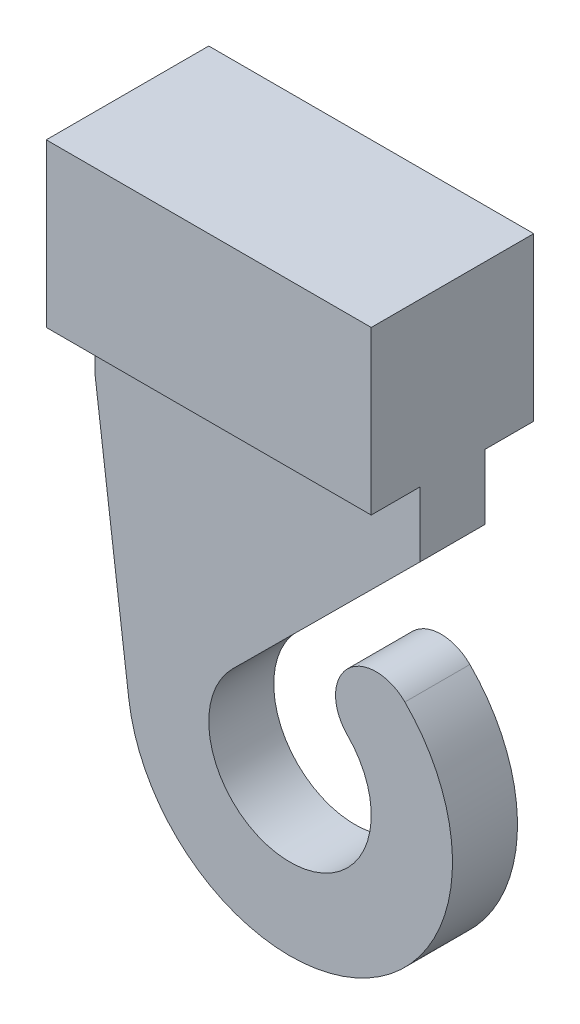
SolidWorks part; units mm, degrees
ref_plane "前视基准面" through (0, 0, 0) normal (0, 0, 1) x (1, 0, 0)
ref_plane "上视基准面" through (0, 0, 0) normal (0, 1, 0) x (1, 0, 0)
ref_plane "右视基准面" through (0, 0, 0) normal (1, 0, 0) x (0, 0, -1)
other "Configuration Table"
sketch "草图1" plane through (0, 0, 0) normal (1, 0, 0) x (0, 0, -1)
  line L1 (-1.5, 1.5) -> (1.5, 1.5)
  line L2 (-1.5, 1.5) -> (-1.5, -1.5)
  line L3 (-1.5, -1.5) -> (1.5, -1.5)
  line L4 (1.5, 1.5) -> (1.5, -1.5)
  line L5 (-1.5, 1.5) -> (1.5, -1.5) construction
  line L6 (-1.5, -1.5) -> (1.5, 1.5) construction
  line L7 (-2.5, 2.5) -> (2.5, 2.5)
  line L8 (-2.5, 2.5) -> (-2.5, -2.5)
  line L9 (-2.5, -2.5) -> (2.5, -2.5)
  line L10 (2.5, 2.5) -> (2.5, -2.5)
  line L11 (-2.5, 2.5) -> (2.5, -2.5) construction
  line L12 (-2.5, -2.5) -> (2.5, 2.5) construction
  point P0 (0, 0)
  point P6 (0, 0)
  dimension "D1" = 3
  dimension "D2" = 3
  dimension "D3" = 5
  dimension "D4" = 5
extrude "凸台-拉伸1" add sketch "草图1" along normal blind 8
sketch "草图2" plane through (8, 0, 0) normal (1, 0, 0) x (0, 0, -1)
  line L4 (2.5, -2.5) -> (2.5, 2.5)
  line L5 (2.5, 2.5) -> (-2.5, 2.5)
  line L6 (-2.5, 2.5) -> (-2.5, -2.5)
  line L7 (-2.5, -2.5) -> (2.5, -2.5)
  line L8 (2.5, -2.5) -> (2.5, 2.5)
  line L9 (2.5, 2.5) -> (-2.5, 2.5)
  line L10 (-2.5, 2.5) -> (-2.5, -2.5)
  line L11 (-2.5, -2.5) -> (2.5, -2.5)
  dimension "D1" = 0
extrude "凸台-拉伸2" add sketch "草图2" along normal blind 2
sketch "草图3" plane through (0, -2.5, 0) normal (0, -1, 0) x (1, 0, 0)
  line L0 (0, 0) -> (10, 0) construction
  line L1 (10, 2.5) -> (10, -2.5) construction
  line L2 (5, 2.5) -> (5, -2.5) construction
  line L3 (10, 2.5) -> (0, 2.5) construction
  line L4 (10, -2.5) -> (0, -2.5) construction
  line L6 (0, 1) -> (10, 1)
  line L7 (0, 1) -> (0, -1)
  line L8 (0, -1) -> (10, -1)
  line L9 (10, 1) -> (10, -1)
  line L10 (0, 1) -> (10, -1) construction
  line L11 (0, -1) -> (10, 1) construction
  point P11 (5, 0)
  dimension "D1" = 2
extrude "凸台-拉伸3" add sketch "草图3" along normal blind 2
sketch "草图4" plane through (0, 0, 1) normal (0, 0, 1) x (1, 0, 0)
  line L0 (0, 0) -> (0, -0.3812) construction
  line L1 (0, 0) -> (10, 0) construction
  line L2 (10, 2.5) -> (10, -2.5) construction
  line L3 (6, 0) -> (6, -12) construction
  line L4 (0, -4.5) -> (10, -4.5)
  line L5 (0, -4.5) -> (1.0404, -12.6343)
  line L6 (10, -4.5) -> (4.2377, -10.2268)
  line L7 (6, -12) -> (9.5355, -8.4645) construction
  line L8 (6, -12) -> (13.2459, -12) construction
  circle A0 centre (6, -12) radius 2.5
  arc A1 (1.0404, -12.6343) -> (9.5355, -8.4645) centre (6, -12) ccw
  circle A2 centre (8.6517, -9.3483) radius 1.25
  arc A3 (7.309, -7.1744) -> (6, -7) centre (6, -12) ccw
  dimension "D3" = 5
  dimension "D4" = 10
  dimension "D5" = 2.5
  dimension "D1" = 12
  dimension "D2" = 4
  dimension "D6" = 45
extrude "凸台-拉伸4" add sketch "草图4" against normal blind 2
